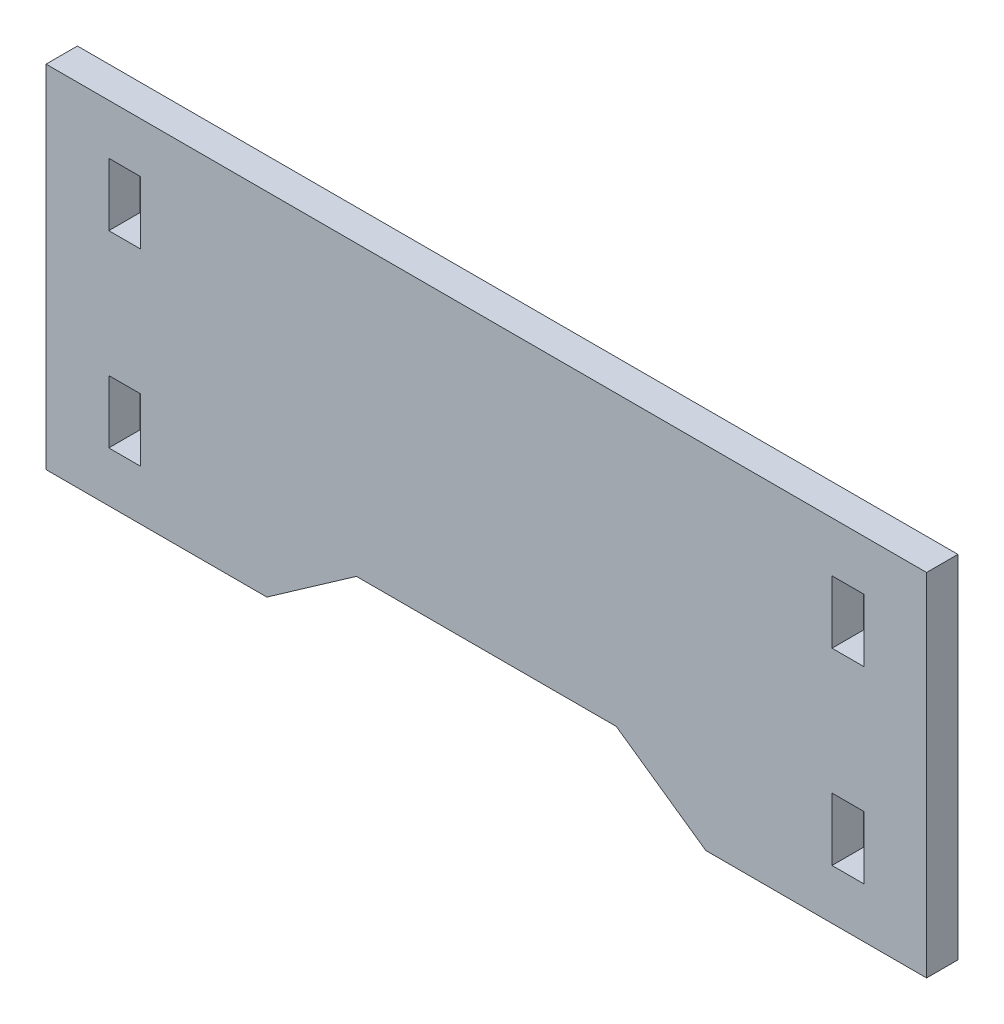
SolidWorks part; units mm, degrees
ref_plane "Front Plane" through (0, 0, 0) normal (0, 0, 1) x (1, 0, 0)
ref_plane "Top Plane" through (0, 0, 0) normal (0, 1, 0) x (1, 0, 0)
ref_plane "Right Plane" through (0, 0, 0) normal (1, 0, 0) x (0, 0, -1)
sketch "Sketch1" plane through (0, 0, 0) normal (0, 0, 1) x (1, 0, 0)
  line L1 (-44.577, -17.78) -> (44.577, -17.78)
  line L2 (-44.577, -17.78) -> (-44.577, 17.78)
  line L3 (-44.577, 17.78) -> (44.577, 17.78)
  line L4 (44.577, -17.78) -> (44.577, 17.78)
  line L5 (-44.577, -17.78) -> (44.577, 17.78) construction
  line L6 (-44.577, 17.78) -> (44.577, -17.78) construction
  point P0 (0, 0)
  dimension "D1" = 89.154
  dimension "D2" = 35.56
extrude "Boss-Extrude1" add sketch "Sketch1" along normal blind 3.175
sketch "Sketch2" plane through (0, 0, 3.175) normal (0, 0, 1) x (1, 0, 0)
  line L0 (-44.577, 0) -> (0, 0) construction
  line L1 (-44.577, 17.78) -> (-44.577, -17.78) construction
  line L3 (-38.227, 12.7) -> (-35.0012, 12.7)
  line L4 (-38.227, 12.7) -> (-38.227, 6.35)
  line L5 (-38.227, 6.35) -> (-35.0012, 6.35)
  line L6 (-35.0012, 12.7) -> (-35.0012, 6.35)
  line L7 (-38.227, 12.7) -> (-35.0012, 6.35) construction
  line L8 (-38.227, 6.35) -> (-35.0012, 12.7) construction
  line L9 (-38.227, -6.35) -> (-35.0012, -6.35)
  line L10 (-38.227, -6.35) -> (-38.227, -12.7)
  line L11 (-38.227, -12.7) -> (-35.0012, -12.7)
  line L12 (-35.0012, -6.35) -> (-35.0012, -12.7)
  line L13 (-38.227, -6.35) -> (-35.0012, -12.7) construction
  line L14 (-38.227, -12.7) -> (-35.0012, -6.35) construction
  point P5 (-36.6141, 9.525)
  point P10 (-36.6141, -9.525)
  dimension "D1" = 6.35
  dimension "D2" = 6.35
  dimension "D3" = 3.2258
  dimension "D4" = 3.2258
  dimension "D5" = 6.35
  dimension "D6" = 6.35
  dimension "D7" = 6.35
  dimension "D8" = 6.35
extrude "Cut-Extrude1" cut sketch "Sketch2" against normal through all
mirror "Mirror1" about plane through (0, 0, 0) normal (1, 0, 0) of "Cut-Extrude1"
sketch "Sketch3" plane through (0, 0, 3.175) normal (0, 0, 1) x (1, 0, 0)
  line L0 (0, -11.43) -> (0, -8.3539) construction
  line L2 (-13.1563, -11.43) -> (13.1563, -11.43)
  line L3 (-13.1563, -11.43) -> (-22.225, -17.78)
  line L4 (-44.577, -17.78) -> (44.577, -17.78) construction
  line L5 (-22.225, -17.78) -> (22.225, -17.78)
  line L6 (22.225, -17.78) -> (13.1563, -11.43)
  dimension "D1" = 35
  dimension "D2" = 35
  dimension "D3" = 6.35
  dimension "D4" = 44.45
extrude "Cut-Extrude2" cut sketch "Sketch3" against normal through all
